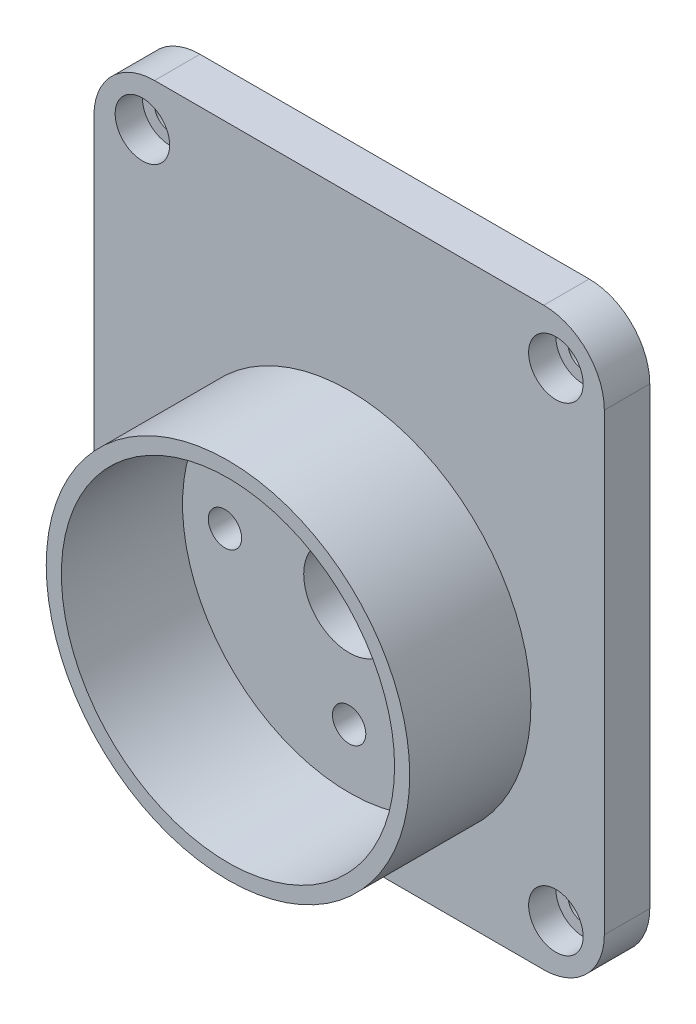
SolidWorks part; units mm, degrees
material "ABS"
ref_plane "Płaszczyzna przednia" through (0, 0, 0) normal (0, 0, 1) x (1, 0, 0)
ref_plane "Płaszczyzna górna" through (0, 0, 0) normal (0, 1, 0) x (1, 0, 0)
ref_plane "Płaszczyzna prawa" through (0, 0, 0) normal (1, 0, 0) x (0, 0, -1)
sketch "Szkic1" plane through (0, 0, 0) normal (0, 0, 1) x (1, 0, 0)
  line L0 (-24.531, 0) -> (41.5648, 0) construction
  line L1 (0, 25.1144) -> (0, -24.8112) construction
  line L2 (-16.85, 0) -> (-16.85, -14.7)
  line L3 (-16.85, -14.7) -> (0, -14.7)
  line L4 (0, -14.7) -> (16.85, -14.7)
  line L5 (16.85, -14.7) -> (16.85, 23.3)
  line L6 (16.85, 23.3) -> (-16.85, 23.3)
  line L7 (-16.85, 23.3) -> (-16.85, 0)
  line L8 (-13.65, 27.1146) -> (-13.65, -20.6837) construction
  line L9 (13.65, 25.9393) -> (13.65, -20.0568) construction
  circle A0 centre (0, 0) radius 3
  circle A1 centre (-8.2, 0) radius 1.1
  circle A2 centre (8.2, 0) radius 1.1
  circle A3 centre (0, 7.1) radius 1.1
  circle A4 centre (0, -7.1) radius 1.1
  circle A5 centre (-13.65, 20.1) radius 1
  circle A6 centre (13.65, 20.1) radius 1
  circle A7 centre (13.65, -11.5) radius 1
  circle A8 centre (-13.65, -11.5) radius 1
  dimension "D3" = 6
  dimension "D9" = 2.2
  dimension "D10" = 2.2
  dimension "D11" = 2.2
  dimension "D12" = 2.2
  dimension "D19" = 2
  dimension "D20" = 2
  dimension "D21" = 2
  dimension "D22" = 2
  dimension "D1" = 38
  dimension "D2" = 33.7
  dimension "D4" = 14.7
  dimension "D5" = 8.2
  dimension "D6" = 8.2
  dimension "D7" = 7.1
  dimension "D8" = 7.1
  dimension "D13" = 3.2
  dimension "D14" = 3.2
  dimension "D15" = 3.2
  dimension "D16" = 3.2
  dimension "D17" = 3.2
  dimension "D18" = 3.2
extrude "Dodanie-wyciągnięcie1" add sketch "Szkic1" along normal blind 3
sketch "Szkic2" plane through (0, 0, 3) normal (0, 0, 1) x (1, 0, 0)
  circle A0 centre (0, 0) radius 12
  circle A1 centre (0, 0) radius 11
  dimension "D1" = 24
  dimension "D2" = 22
extrude "Dodanie-wyciągnięcie2" add sketch "Szkic2" along normal blind 8
sketch "Szkic3" plane through (0, 0, 0) normal (0, 0, -1) x (-1, 0, 0)
  line L0 (-15.85, 27.4391) -> (-15.85, -18.66)
  line L1 (15.85, 26.9614) -> (15.85, -19.914)
  line L2 (-25.3784, -13.7) -> (25.1395, -13.7)
  line L3 (-22.9301, 22.3) -> (20.3027, 22.3)
  line L4 (-16.85, 23.3) -> (16.85, 23.3) construction
  line L5 (-16.85, -14.7) -> (-16.85, 23.3) construction
  line L6 (16.85, 23.3) -> (16.85, -14.7) construction
  line L7 (16.85, -14.7) -> (-16.85, -14.7) construction
  line L8 (-16.85, -14.7) -> (-16.85, 23.3)
  line L9 (-16.85, 23.3) -> (16.85, 23.3)
  line L10 (16.85, 23.3) -> (16.85, -14.7)
  line L11 (16.85, -14.7) -> (-16.85, -14.7)
  circle A0 centre (-13.65, 20.1) radius 3.2
  circle A1 centre (13.65, 20.1) radius 3.2
  circle A2 centre (-13.65, -11.5) radius 3.2
  circle A3 centre (13.65, -11.5) radius 3.2
  circle M9 centre (0, 0) radius 3
  circle M10 centre (8.2, 0) radius 1.1
  circle M11 centre (-8.2, 0) radius 1.1
  circle M12 centre (0, 7.1) radius 1.1
  circle M13 centre (0, -7.1) radius 1.1
  dimension "D5" = 6.4
  dimension "D6" = 6.4
  dimension "D7" = 6.4
  dimension "D8" = 6.4
  dimension "D1" = 1
  dimension "D2" = 1
  dimension "D3" = 1
  dimension "D4" = 1
extrude "Wytnij-wyciągnięcie1" cut sketch "Szkic3" against normal blind 1 contours A3 L1 A1 L3 A0 L0 A2 L2 M9 M11 M13 M12 M10
sketch "Szkic4" plane through (0, 0, 3) normal (0, 0, 1) x (1, 0, 0)
  circle A0 centre (-13.65, 20.1) radius 1.8
  circle A1 centre (13.65, 20.1) radius 1.8
  circle A2 centre (13.65, -11.5) radius 1.8
  circle A3 centre (-13.65, -11.5) radius 1.8
  dimension "D1" = 3.6
  dimension "D2" = 3.6
  dimension "D3" = 3.6
  dimension "D4" = 3.6
extrude "Wytnij-wyciągnięcie2" cut sketch "Szkic4" against normal blind 1.8
fillet "Zaokrąglenie1" radius 4 4 edges at (-16.85, 23.3, 1.5) (-16.85, -14.7, 1.5) (16.85, -14.7, 1.5) (16.85, 23.3, 1.5)
